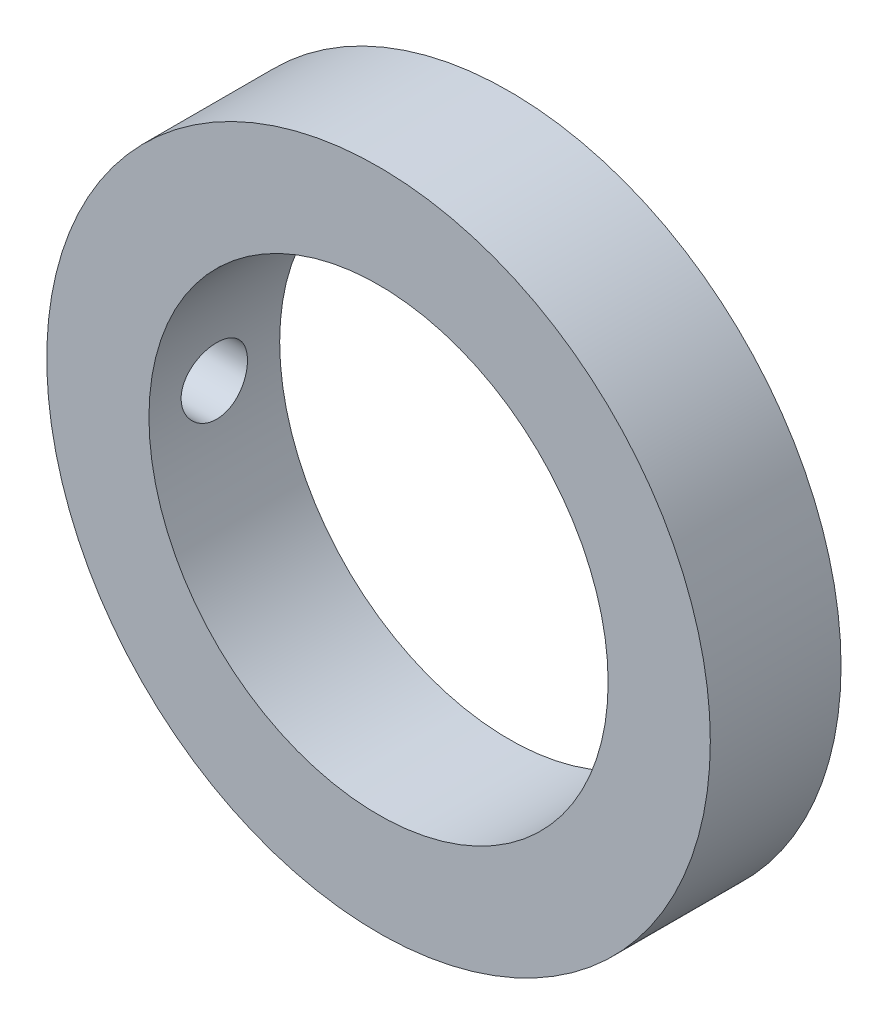
SolidWorks part; units mm, degrees
material "AISI 1045 Aço, trefilado"
ref_plane "Plano frontal" through (0, 0, 0) normal (0, 0, 1) x (1, 0, 0)
ref_plane "Plano superior" through (0, 0, 0) normal (0, 1, 0) x (1, 0, 0)
ref_plane "Plano direito" through (0, 0, 0) normal (1, 0, 0) x (0, 0, -1)
sketch "Esboço1" plane through (0, 0, 0) normal (0, 0, 1) x (1, 0, 0)
  circle A0 centre (0, 0) radius 17.3
  circle A1 centre (0, 0) radius 25
  dimension "D1" = 50
  dimension "D2" = 34.6
extrude "Ressalto-extrusão1" add sketch "Esboço1" along normal blind 9.85
sketch "Esboço2" plane through (0, 0, 0) normal (1, 0, 0) x (0, 0, -1)
  line L0 (0, 0) -> (-9.85, 0) construction
  line L1 (-9.85, 25) -> (-9.85, -25) construction
  circle A0 centre (-4.925, 0) radius 2.5
  dimension "D1" = 5
extrude "Corte-extrusão1" cut sketch "Esboço2" against normal through all
cosmetic thread "Representação de rosca1" parameters "D1"=5, "D2"=6
